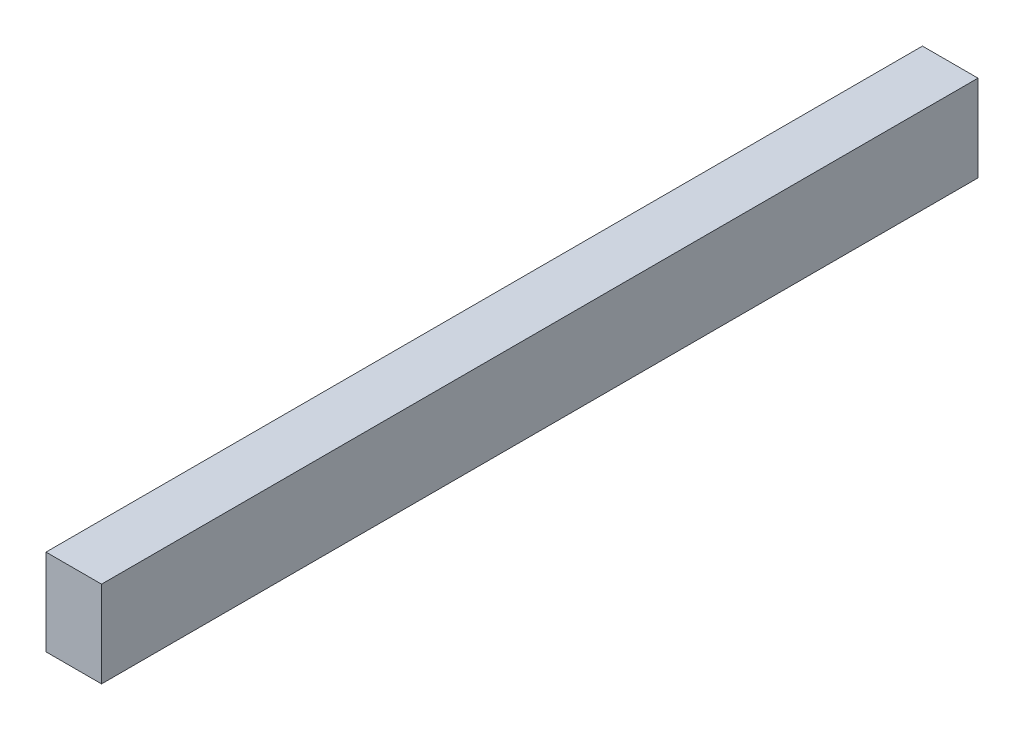
SolidWorks part; units mm, degrees
material "Pine"
ref_plane "Front Plane" through (0, 0, 0) normal (0, 0, 1) x (1, 0, 0)
ref_plane "Top Plane" through (0, 0, 0) normal (0, 1, 0) x (1, 0, 0)
ref_plane "Right Plane" through (0, 0, 0) normal (1, 0, 0) x (0, 0, -1)
sketch "Sketch1" plane through (0, 0, 0) normal (0, 0, 1) x (1, 0, 0)
  line L1 (0, 0) -> (45, 0)
  line L2 (0, 0) -> (0, -70)
  line L3 (0, -70) -> (45, -70)
  line L4 (45, 0) -> (45, -70)
  dimension "D1" = 45
  dimension "D2" = 70
extrude "Boss-Extrude1" add sketch "Sketch1" along normal blind 710
